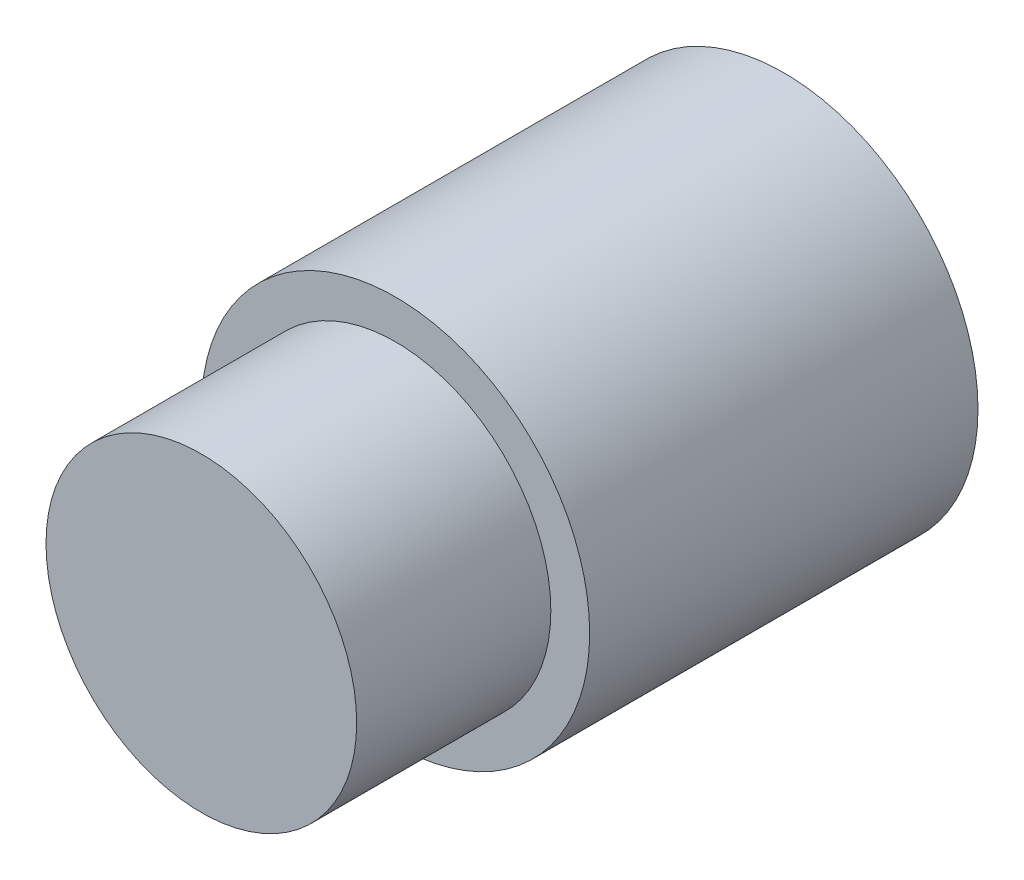
SolidWorks part; units mm, degrees
ref_plane "정면" through (0, 0, 0) normal (0, 0, 1) x (1, 0, 0)
ref_plane "윗면" through (0, 0, 0) normal (0, 1, 0) x (1, 0, 0)
ref_plane "우측면" through (0, 0, 0) normal (1, 0, 0) x (0, 0, -1)
sketch "스케치1" plane through (0, 0, 0) normal (0, 0, 1) x (1, 0, 0)
  circle A0 centre (0, 0) radius 10
  dimension "D1" = 20
extrude "보스-돌출1" add sketch "스케치1" along normal blind 20
ref_plane "평면1" through (0, 0, 0) normal (0, 0, -1) x (-1, 0, 0)
sketch "스케치2" plane through (0, 0, 0) normal (0, 0, -1) x (-1, 0, 0)
  circle A0 centre (0, 0) radius 1.5
  dimension "D1" = 3
extrude "컷-돌출1" cut sketch "스케치2" against normal blind 10
ref_plane "평면2" through (0, 0, 20) normal (0, 0, 1) x (1, 0, 0)
sketch "스케치3" plane through (0, 0, 20) normal (0, 0, 1) x (1, 0, 0)
  circle A0 centre (0, 0) radius 8
  dimension "D1" = 16
extrude "보스-돌출2" add sketch "스케치3" along normal blind 10
